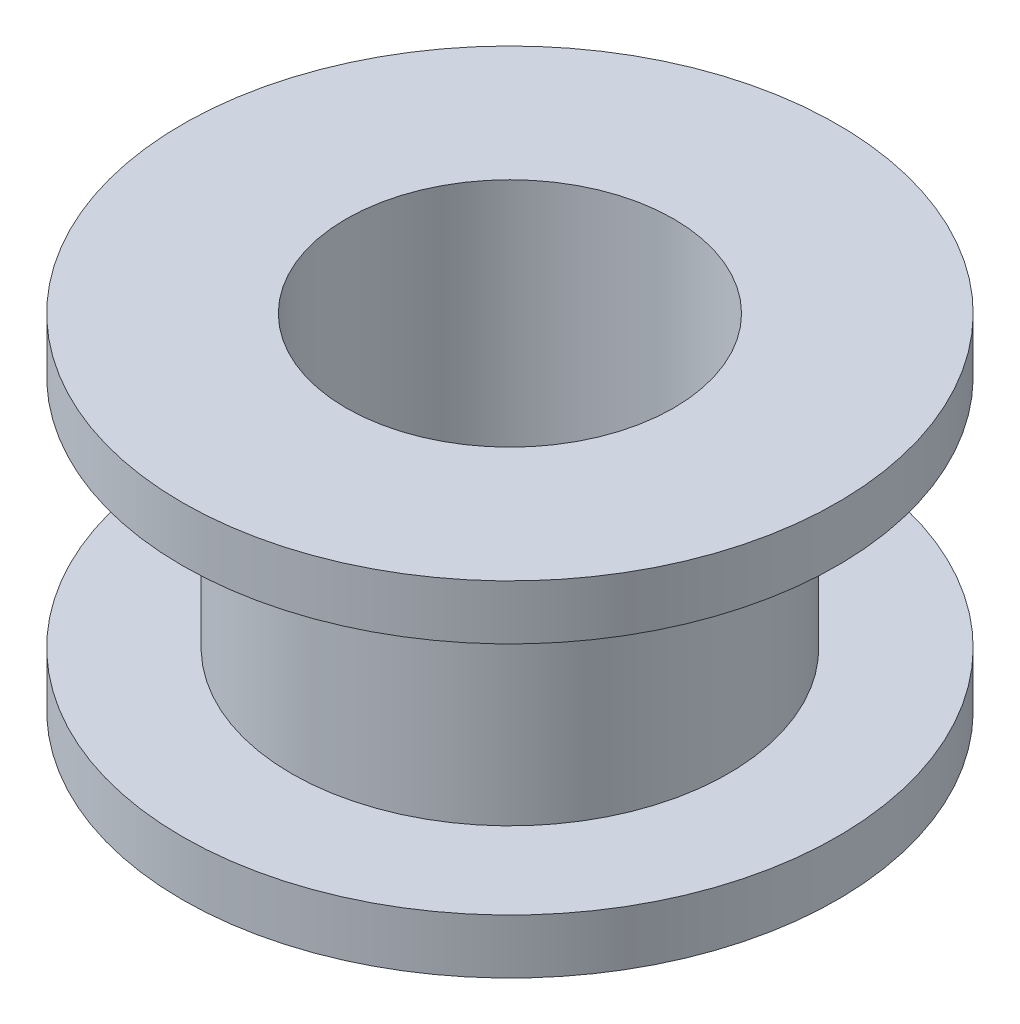
SolidWorks part; units mm, degrees
material "6061 Alloy"
ref_plane "Front Plane" through (0, 0, 0) normal (0, 0, 1) x (1, 0, 0)
ref_plane "Top Plane" through (0, 0, 0) normal (0, 1, 0) x (1, 0, 0)
ref_plane "Right Plane" through (0, 0, 0) normal (1, 0, 0) x (0, 0, -1)
sketch "Sketch1" plane through (0, 0, 0) normal (0, 1, 0) x (1, 0, 0)
  circle A0 centre (0, 0) radius 6
  circle A1 centre (0, 0) radius 4.5
  dimension "D1" = 9
  dimension "D2" = 12
extrude "Boss-Extrude1" add sketch "Sketch1" along normal mid plane 6.45
sketch "Sketch2" plane through (0, 3.225, 0) normal (0, 1, 0) x (1, 0, 0)
  circle A0 centre (0, 0) radius 9
  circle A1 centre (0, 0) radius 4.5
  circle A2 centre (0, 0) radius 4.5 construction
  dimension "D1" = 18
extrude "Boss-Extrude2" add sketch "Sketch2" along normal blind 1.5
mirror "Mirror1" about plane through (0, 0, 0) normal (0, 1, 0) of "Boss-Extrude2"
